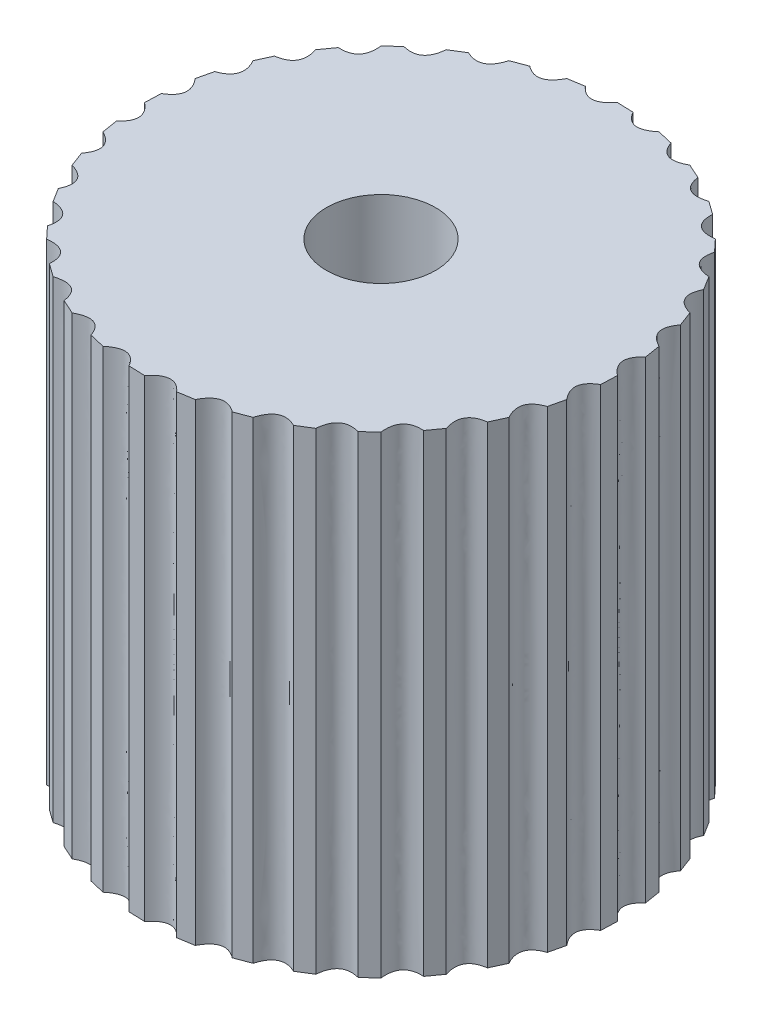
SolidWorks part; units mm, degrees
material "1060-H12"
ref_plane "前视基准面" through (0, 0, 0) normal (0, 0, 1) x (1, 0, 0)
ref_plane "上视基准面" through (0, 0, 0) normal (0, 1, 0) x (1, 0, 0)
ref_plane "右视基准面" through (0, 0, 0) normal (1, 0, 0) x (0, 0, -1)
other "Configuration Table"
sketch "草图1" plane through (0, 0, 0) normal (0, 1, 0) x (1, 0, 0)
  spline S0 degree 2 poles (-6.5, 0) (-5.9842, -0.4167) (-6.4469, -0.829) knots 0 0 0 1 1 1
  spline S1 degree 2 poles (-6.3751, 1.2681) (-5.9505, 0.7588) (-6.4848, 0.4447) knots 0 0 0 1 1 1
  spline S2 degree 2 poles (-6.0052, 2.4874) (-5.6881, 1.9051) (-6.2734, 1.7013) knots 0 0 0 1 1 1
  spline S3 degree 2 poles (-5.4046, 3.6112) (-5.2072, 2.9782) (-5.821, 2.8925) knots 0 0 0 1 1 1
  spline S4 degree 2 poles (-4.5962, 4.5962) (-4.5261, 3.9368) (-5.1448, 3.9725) knots 0 0 0 1 1 1
  spline S5 degree 2 poles (-3.6112, 5.4046) (-3.6711, 4.7442) (-4.271, 4.8999) knots 0 0 0 1 1 1
  spline S6 degree 2 poles (-2.4874, 6.0052) (-2.675, 5.3692) (-3.233, 5.6389) knots 0 0 0 1 1 1
  spline S7 degree 2 poles (-1.2681, 6.3751) (-1.5761, 5.7879) (-2.0708, 6.1613) knots 0 0 0 1 1 1
  spline S8 degree 2 poles (0, 6.5) (-0.4167, 5.9842) (-0.829, 6.4469) knots 0 0 0 1 1 1
  spline S9 degree 2 poles (1.2681, 6.3751) (0.7588, 5.9505) (0.4447, 6.4848) knots 0 0 0 1 1 1
  spline S10 degree 2 poles (2.4874, 6.0052) (1.9051, 5.6881) (1.7013, 6.2734) knots 0 0 0 1 1 1
  spline S11 degree 2 poles (3.6112, 5.4046) (2.9782, 5.2072) (2.8925, 5.821) knots 0 0 0 1 1 1
  spline S12 degree 2 poles (4.5962, 4.5962) (3.9368, 4.5261) (3.9725, 5.1448) knots 0 0 0 1 1 1
  spline S13 degree 2 poles (5.4046, 3.6112) (4.7442, 3.6711) (4.8999, 4.271) knots 0 0 0 1 1 1
  spline S14 degree 2 poles (6.0052, 2.4874) (5.3692, 2.675) (5.6389, 3.233) knots 0 0 0 1 1 1
  spline S15 degree 2 poles (6.3751, 1.2681) (5.7879, 1.5761) (6.1613, 2.0708) knots 0 0 0 1 1 1
  spline S16 degree 2 poles (6.5, 0) (5.9842, 0.4167) (6.4469, 0.829) knots 0 0 0 1 1 1
  spline S17 degree 2 poles (6.3751, -1.2681) (5.9505, -0.7588) (6.4848, -0.4447) knots 0 0 0 1 1 1
  spline S18 degree 2 poles (6.0052, -2.4874) (5.6881, -1.9051) (6.2734, -1.7013) knots 0 0 0 1 1 1
  spline S19 degree 2 poles (5.4046, -3.6112) (5.2072, -2.9782) (5.821, -2.8925) knots 0 0 0 1 1 1
  spline S20 degree 2 poles (4.5962, -4.5962) (4.5261, -3.9368) (5.1448, -3.9725) knots 0 0 0 1 1 1
  spline S21 degree 2 poles (3.6112, -5.4046) (3.6711, -4.7442) (4.271, -4.8999) knots 0 0 0 1 1 1
  spline S22 degree 2 poles (2.4874, -6.0052) (2.675, -5.3692) (3.233, -5.6389) knots 0 0 0 1 1 1
  spline S23 degree 2 poles (1.2681, -6.3751) (1.5761, -5.7879) (2.0708, -6.1613) knots 0 0 0 1 1 1
  spline S24 degree 2 poles (0, -6.5) (0.4167, -5.9842) (0.829, -6.4469) knots 0 0 0 1 1 1
  spline S25 degree 2 poles (-1.2681, -6.3751) (-0.7588, -5.9505) (-0.4447, -6.4848) knots 0 0 0 1 1 1
  spline S26 degree 2 poles (-2.4874, -6.0052) (-1.9051, -5.6881) (-1.7013, -6.2734) knots 0 0 0 1 1 1
  spline S27 degree 2 poles (-3.6112, -5.4046) (-2.9782, -5.2072) (-2.8925, -5.821) knots 0 0 0 1 1 1
  spline S28 degree 2 poles (-4.5962, -4.5962) (-3.9368, -4.5261) (-3.9725, -5.1448) knots 0 0 0 1 1 1
  spline S29 degree 2 poles (-5.4046, -3.6112) (-4.7442, -3.6711) (-4.8999, -4.271) knots 0 0 0 1 1 1
  spline S30 degree 2 poles (-6.0052, -2.4874) (-5.3692, -2.675) (-5.6389, -3.233) knots 0 0 0 1 1 1
  spline S31 degree 2 poles (-6.3751, -1.2681) (-5.7879, -1.5761) (-6.1613, -2.0708) knots 0 0 0 1 1 1
  spline S32 degree 1 poles (-6.3751, 1.2681) (-6.2734, 1.7013) knots 0 0 1 1
  spline S33 degree 1 poles (-6.4848, 0.4447) (-6.5, 0) knots 0 0 1 1
  spline S34 degree 1 poles (-6.4469, -0.829) (-6.3751, -1.2681) knots 0 0 1 1
  spline S35 degree 1 poles (-6.1613, -2.0708) (-6.0052, -2.4874) knots 0 0 1 1
  spline S36 degree 1 poles (-5.6389, -3.233) (-5.4046, -3.6112) knots 0 0 1 1
  spline S37 degree 1 poles (-4.8999, -4.271) (-4.5962, -4.5962) knots 0 0 1 1
  spline S38 degree 1 poles (-3.9725, -5.1448) (-3.6112, -5.4046) knots 0 0 1 1
  spline S39 degree 1 poles (-2.8925, -5.821) (-2.4874, -6.0052) knots 0 0 1 1
  spline S40 degree 1 poles (-1.7013, -6.2734) (-1.2681, -6.3751) knots 0 0 1 1
  spline S41 degree 1 poles (-0.4447, -6.4848) (0, -6.5) knots 0 0 1 1
  spline S42 degree 1 poles (0.829, -6.4469) (1.2681, -6.3751) knots 0 0 1 1
  spline S43 degree 1 poles (2.0708, -6.1613) (2.4874, -6.0052) knots 0 0 1 1
  spline S44 degree 1 poles (3.233, -5.6389) (3.6112, -5.4046) knots 0 0 1 1
  spline S45 degree 1 poles (4.271, -4.8999) (4.5962, -4.5962) knots 0 0 1 1
  spline S46 degree 1 poles (5.1448, -3.9725) (5.4046, -3.6112) knots 0 0 1 1
  spline S47 degree 1 poles (5.821, -2.8925) (6.0052, -2.4874) knots 0 0 1 1
  spline S48 degree 1 poles (6.3751, -1.2681) (6.2734, -1.7013) knots 0 0 1 1
  spline S49 degree 1 poles (6.5, 0) (6.4848, -0.4447) knots 0 0 1 1
  spline S50 degree 1 poles (6.3751, 1.2681) (6.4469, 0.829) knots 0 0 1 1
  spline S51 degree 1 poles (6.0052, 2.4874) (6.1613, 2.0708) knots 0 0 1 1
  spline S52 degree 1 poles (5.4046, 3.6112) (5.6389, 3.233) knots 0 0 1 1
  spline S53 degree 1 poles (4.5962, 4.5962) (4.8999, 4.271) knots 0 0 1 1
  spline S54 degree 1 poles (3.6112, 5.4046) (3.9725, 5.1448) knots 0 0 1 1
  spline S55 degree 1 poles (2.4874, 6.0052) (2.8925, 5.821) knots 0 0 1 1
  spline S56 degree 1 poles (1.2681, 6.3751) (1.7013, 6.2734) knots 0 0 1 1
  spline S57 degree 1 poles (0, 6.5) (0.4447, 6.4848) knots 0 0 1 1
  spline S58 degree 1 poles (-1.2681, 6.3751) (-0.829, 6.4469) knots 0 0 1 1
  spline S59 degree 1 poles (-2.4874, 6.0052) (-2.0708, 6.1613) knots 0 0 1 1
  spline S60 degree 1 poles (-3.6112, 5.4046) (-3.233, 5.6389) knots 0 0 1 1
  spline S61 degree 1 poles (-4.5962, 4.5962) (-4.271, 4.8999) knots 0 0 1 1
  spline S62 degree 1 poles (-5.1448, 3.9725) (-5.4046, 3.6112) knots 0 0 1 1
  spline S63 degree 1 poles (-5.821, 2.8925) (-6.0052, 2.4874) knots 0 0 1 1
  point P102 (0, 0)
extrude "凸台-拉伸1" add sketch "草图1" along normal blind 13
sketch "草图2" plane through (0, 13, 0) normal (0, 1, 0) x (1, 0, 0)
  circle A0 centre (0, 0) radius 1.5
extrude "切除-拉伸1" cut sketch "草图2" against normal blind 12
